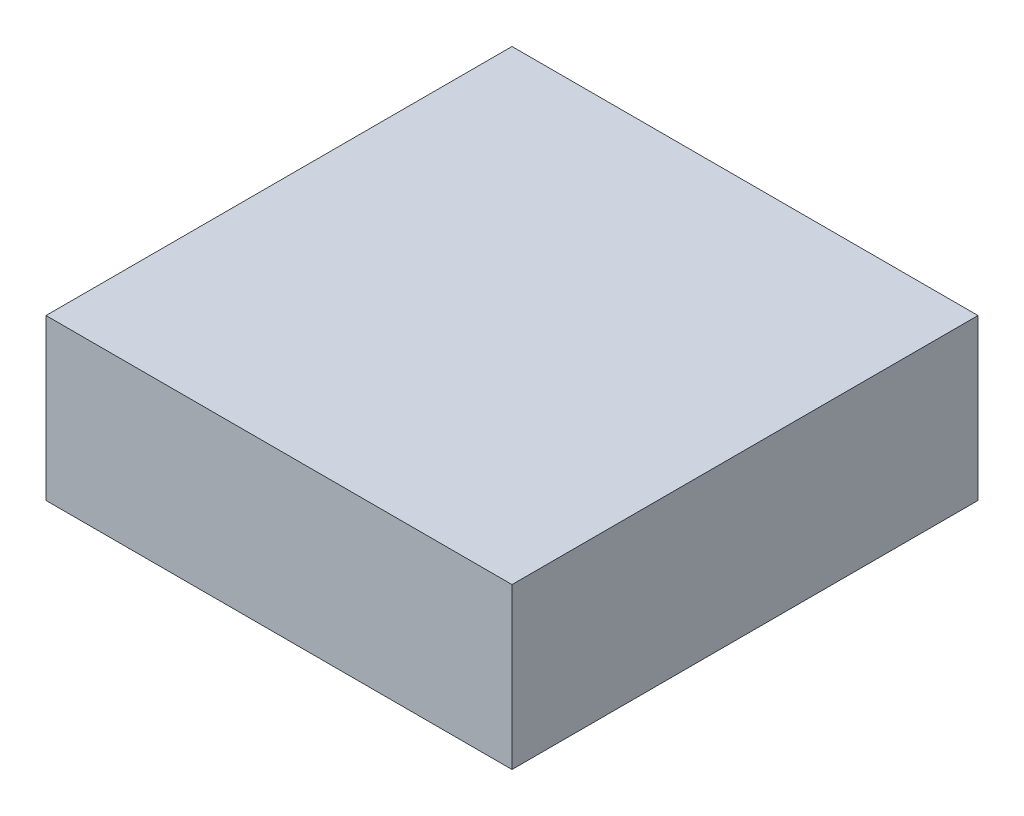
SolidWorks part; units mm, degrees
ref_plane "Alzado" through (0, 0, 0) normal (0, 0, 1) x (1, 0, 0)
ref_plane "Planta" through (0, 0, 0) normal (0, 1, 0) x (1, 0, 0)
ref_plane "Vista lateral" through (0, 0, 0) normal (1, 0, 0) x (0, 0, -1)
sketch "Croquis1" plane through (0, 0, 0) normal (0, 0, 1) x (1, 0, 0)
  line L0 (-51.9597, 14.1482) -> (-51.9597, 3.1482)
  line L1 (-51.9597, 14.1482) -> (-19.9597, 14.1482)
  line L2 (-19.9597, 14.1482) -> (-19.9597, 3.1482)
  line L3 (-19.9597, 3.1482) -> (-35.9597, -4.2902)
  line L4 (-35.9597, -4.2902) -> (-51.9597, 3.1482)
extrude "Saliente-Extruir1" add sketch "Croquis1" along normal blind 32
sketch "Croquis2" plane through (-19.9597, 0, 0) normal (1, 0, 0) x (0, 0, -1)
  line L5 (-32, 14.1482) -> (-32, 3.1482)
  line L6 (-32, 3.1482) -> (-16, -4.2902)
  line L7 (-32, -4.2902) -> (0, -4.2902) construction
  line L8 (-16, -4.2902) -> (-32, -4.2902)
  line L9 (-32, -4.2902) -> (-32, 3.1482)
  line L10 (-16, -4.2902) -> (0, 3.1482)
  line L11 (0, 3.1482) -> (0, -4.2902)
  line L12 (0, -4.2902) -> (-16, -4.2902)
extrude "Cortar-Extruir1" cut sketch "Croquis2" against normal blind 33 contours L12 L11 L10 | L9 L8 L6
sketch "Croquis4" plane through (-4.7507, 10.2188, 0) normal (0.4216, -0.9068, 0) x (-0.9068, -0.4216, 0)
  line L0 (16.7722, -32) -> (16.7722, -16)
  line L1 (16.7722, -32) -> (16.7722, 0) construction
  line L2 (16.7722, -16) -> (20.7722, -16)
  circle A0 centre (20.7722, -16) radius 1
extrude "Saliente-Extruir2" add sketch "Croquis4" along normal blind 0.005 contours A0
